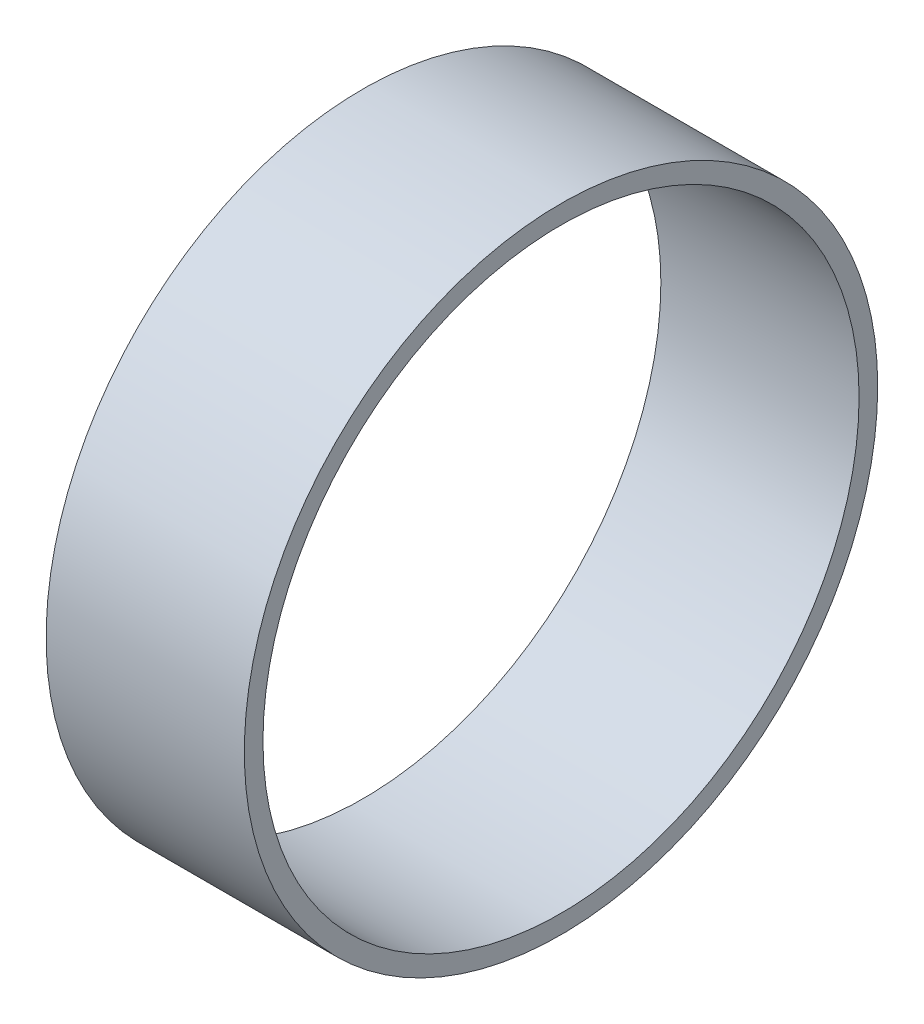
SolidWorks part; units mm, degrees
material "PVC Rigid"
ref_plane "Front Plane" through (0, 0, 0) normal (0, 0, 1) x (1, 0, 0)
ref_plane "Top Plane" through (0, 0, 0) normal (0, 1, 0) x (1, 0, 0)
ref_plane "Right Plane" through (0, 0, 0) normal (1, 0, 0) x (0, 0, -1)
sketch "Sketch1" plane through (0, 0, 0) normal (1, 0, 0) x (0, 0, -1)
  circle A0 centre (0, 0) radius 53.975
  circle A1 centre (0, 0) radius 50.8
  dimension "D1" = 101.6
  dimension "D2" = 3.175
extrude "Boss-Extrude1" add sketch "Sketch1" along normal blind 33.782
